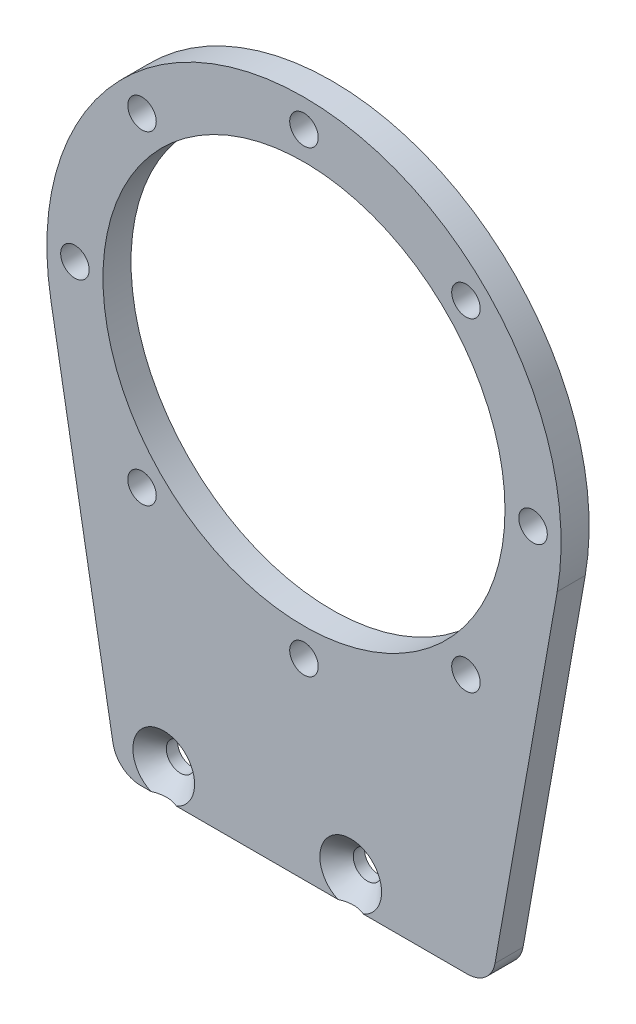
SolidWorks part; units mm, degrees
material "Thornel Mat VMA"
ref_plane "前视基准面" through (0, 0, 0) normal (0, 0, 1) x (1, 0, 0)
ref_plane "上视基准面" through (0, 0, 0) normal (0, 1, 0) x (1, 0, 0)
ref_plane "右视基准面" through (0, 0, 0) normal (1, 0, 0) x (0, 0, -1)
sketch "草图1" plane through (0, 0, 0) normal (0, 0, 1) x (1, 0, 0)
  line L0 (0, 0) -> (0, -45) construction
  line L1 (-20, -45) -> (20, -45)
  line L2 (-20, -45) -> (-27.0834, -4.7685)
  line L3 (20, -45) -> (27.0834, -4.7685)
  circle A0 centre (0, 0) radius 21 construction
  arc A1 (27.0834, -4.7685) -> (-27.0834, -4.7685) centre (0, 0) ccw
  point P8 (0, -45)
  dimension "D1" = 42
  dimension "D2" = 6.5
  dimension "D3" = 40
  dimension "D4" = 45
extrude "凸台-拉伸1" add sketch "草图1" along normal blind 3
sketch "草图2" plane through (0, 0, 3) normal (0, 0, 1) x (1, 0, 0)
  circle A0 centre (0, 0) radius 21.5
  arc A1 (27.0834, -4.7685) -> (-27.0834, -4.7685) centre (0, 0) ccw construction
  dimension "D1" = 6
extrude "切除-拉伸1" cut sketch "草图2" against normal blind 3
sketch "草图3" plane through (0, 0, 3) normal (0, 0, 1) x (1, 0, 0)
  line L0 (0, 0) -> (0, 24.5) construction
  line L1 (0, 0) -> (17.3241, 17.3241) construction
  circle A0 centre (0, 0) radius 24.5 construction
  circle A1 centre (0, 0) radius 21.5 construction
  circle A2 centre (17.3241, 17.3241) radius 1.525
  circle A3 centre (24.5, 0) radius 1.525
  circle A4 centre (17.3241, -17.3241) radius 1.525
  circle A5 centre (0, -24.5) radius 1.525
  circle A6 centre (-17.3241, -17.3241) radius 1.525
  circle A7 centre (-24.5, 0) radius 1.525
  circle A8 centre (-17.3241, 17.3241) radius 1.525
  circle A9 centre (0, 24.5) radius 1.525
  point P24 (0, 0)
  dimension "D1" = 3
  dimension "D3" = 3.05
  dimension "D2" = 45
  dimension "D4" = 8
extrude "切除-拉伸2" cut sketch "草图3" against normal blind 3
fillet "圆角1" radius 3 2 edges at (-20, -45, 1.5) (20, -45, 1.5)
sketch "草图4" plane through (0, 0, 3) normal (0, 0, 1) x (1, 0, 0)
  circle A0 centre (-15, -42) radius 1.25 construction
  circle A1 centre (-15, -42) radius 1.25 construction
  circle A2 centre (5, -42) radius 1.25 construction
  circle A3 centre (5, -42) radius 1.25 construction
  circle A4 centre (-15, -42) radius 1.515
  circle A5 centre (5, -42) radius 1.515
  dimension "D1" = 3.03
extrude "切除-拉伸3" cut sketch "草图4" against normal blind 10
hole_wizard "M3 十字槽沉头木螺钉的锥形沉头孔1" positions "草图5" profile "草图6" countersink size "M3" standard "GB"
sketch "草图5" plane through (0, 0, 3) normal (0, 0, 1) x (1, 0, 0)
  point P0 (-15, -42)
  point P3 (5, -42)
sketch "草图6" plane through (-15, -42, 3) normal (1, 0, 0) x (0, -1, 0)
  line L0 (0, 0) -> (0, 8.1513)
  line L1 (0, 8.1513) -> (1.5, 7.25)
  line L2 (1.5, 7.25) -> (1.5, 1.8)
  line L3 (1.5, 1.8) -> (3.3, 0)
  line L5 (3.3, 0) -> (0, 0)
  line L6 (-1.5, 1.8) -> (-3.3, 0) construction
  line L10 (0, 8.1513) -> (-1.5, 7.25) construction
  line L11 (0, -6.35) -> (0, 107.95) construction
  dimension "孔直径" = 3
  dimension "孔深度" = 7.25
  dimension "近端锥形沉头孔直径" = 6.6
  dimension "近端锥形沉头孔角度" = 90
  dimension "导头角度" = 118
